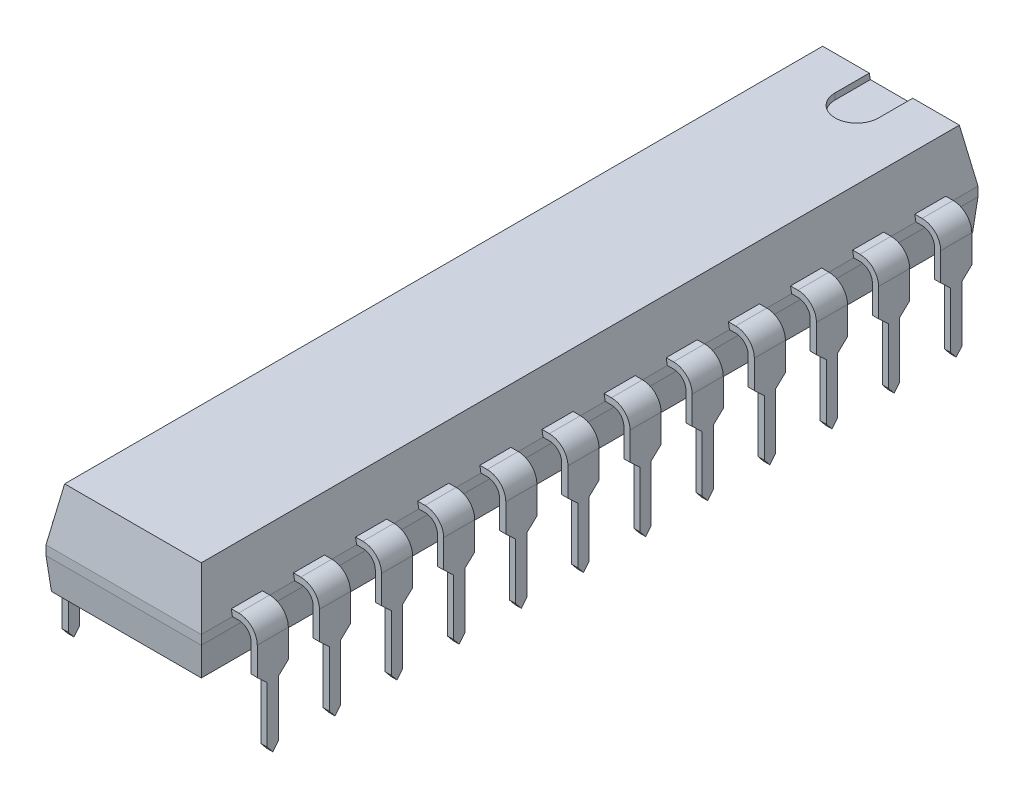
SolidWorks part; units mm, degrees
ref_plane "Front Plane" through (0, 0, 0) normal (0, 0, 1) x (1, 0, 0)
ref_plane "Top Plane" through (0, 0, 0) normal (0, 1, 0) x (1, 0, 0)
ref_plane "Right Plane" through (0, 0, 0) normal (1, 0, 0) x (0, 0, -1)
ref_plane "Plane4" through (0, 0.381, 0) normal (0, 1, 0) x (-1, 0, 0)
sketch "Sketch2" plane through (0, 0.381, 0) normal (0, 1, 0) x (0, 0, 1)
  line L1 (-1.905, 7.112) -> (29.845, 7.112)
  line L2 (-1.905, 7.112) -> (-1.905, 0.762)
  line L3 (-1.905, 0.762) -> (29.845, 0.762)
  line L4 (29.845, 7.112) -> (29.845, 0.762)
  dimension "D1" = 6.35
  dimension "D2" = 31.75
  dimension "D3" = 1.905
  dimension "D4" = 0.762
extrude "Base-Extrude" add sketch "Sketch2" along normal blind 3.81
chamfer "Chamfer1" distance 2.159 angle 10 4 edges at (3.937, 4.191, 29.845) (7.112, 4.191, 13.97) (3.937, 4.191, -1.905) (0.762, 4.191, 13.97)
chamfer "Chamfer2" distance 1.27 angle 5 4 edges at (7.112, 0.381, 13.97) (3.937, 0.381, 29.845) (0.762, 0.381, 13.97) (3.937, 0.381, -1.905)
sketch "Sketch3" plane through (0, 4.191, 0) normal (0, 1, 0) x (-1, 0, 0)
  line L0 (-0.762, -1.905) -> (-7.112, -1.905) construction
  line L1 (-3.048, -1.905) -> (-4.826, -1.905)
  line L2 (-3.937, -1.905) -> (-3.937, 1.8103) construction
  line L3 (-3.048, -1.905) -> (-3.048, -0.127)
  line L4 (-0.762, 29.845) -> (-0.762, -1.905) construction
  line L5 (-4.826, -1.905) -> (-4.826, -0.127)
  arc A0 (-3.048, -0.127) -> (-4.826, -0.127) centre (-3.937, -0.127) ccw
  dimension "D2" = 0.889
  dimension "D1" = 1.778
  dimension "D3" = 1.778
  dimension "D4" = 3.175
extrude "Cut-Extrude1" cut sketch "Sketch3" against normal blind 0.254
sketch "Sketch4" plane through (0, 0, 0) normal (0, 0, -1) x (-1, 0, 0)
  line L0 (-1.1903, 2.032) -> (-0.508, 2.032)
  line L1 (-0.762, 2.032) -> (-7.112, 2.032) construction
  line L2 (0, 1.524) -> (0, -2.5654)
  arc A0 (-0.508, 2.032) -> (0, 1.524) centre (-0.508, 1.524) cw
  dimension "D1" = 0.508
  dimension "D2" = 2.5654
extrude "Boss-Extrude-Thin1" add sketch "Sketch4" along normal mid plane 1.27 thin thin type one direction reverse wall 0.254
sketch "Sketch5" plane through (0, 0, 0) normal (1, 0, 0) x (0, 0, -1)
  line L0 (0.635, -2.5654) -> (-0.635, -2.5654) construction
  line L1 (-0.635, 1.524) -> (-0.635, -2.5654) construction
  line L2 (0, -2.5654) -> (-0.635, -2.5654)
  line L3 (-0.635, 0.381) -> (-0.635, -2.5654)
  line L4 (-0.635, 0.381) -> (-0.2286, 0)
  line L5 (-0.2286, 0) -> (-0.2286, -2.286)
  line L6 (-0.2286, -2.286) -> (0, -2.5654)
  line L7 (50, 0.381) -> (-50, 0.381) construction
  dimension "D1" = 0.2286
  dimension "D2" = 2.286
extrude "Cut-Extrude2" cut sketch "Sketch5" against normal through all
mirror "Mirror1" about plane through (0, 0, 0) normal (0, 0, 1) of "Cut-Extrude2"
ref_plane "Plane5" through (3.937, 0, 0) normal (-1, 0, 0) x (0, 0, 1)
pattern_linear "LPattern1" count 12 spacing 2.54 along (0, 0, 1) of "Cut-Extrude2", "Mirror1", "Boss-Extrude-Thin1"
mirror "Mirror2" about plane through (3.937, 0, 0) normal (-1, 0, 0) of "LPattern1", "Boss-Extrude-Thin1", "Cut-Extrude2", "Mirror1"
sketch "Component_Outline" plane through (0, 0, 0) normal (0, 1, 0) x (1, 0, 0)
  line L0 (0.762, -29.845) -> (0.762, -28.575)
  line L1 (0.762, -28.575) -> (-0.254, -28.575)
  line L2 (-0.254, -28.575) -> (-0.254, -27.305)
  line L3 (-0.254, -27.305) -> (0.762, -27.305)
  line L4 (0.762, -27.305) -> (0.762, -26.035)
  line L5 (0.762, -26.035) -> (-0.254, -26.035)
  line L6 (-0.254, -26.035) -> (-0.254, -24.765)
  line L7 (-0.254, -24.765) -> (0.762, -24.765)
  line L8 (0.762, -24.765) -> (0.762, -23.495)
  line L9 (0.762, -23.495) -> (-0.254, -23.495)
  line L10 (-0.254, -23.495) -> (-0.254, -22.225)
  line L11 (-0.254, -22.225) -> (0.762, -22.225)
  line L12 (0.762, -22.225) -> (0.762, -20.955)
  line L13 (0.762, -20.955) -> (-0.254, -20.955)
  line L14 (-0.254, -20.955) -> (-0.254, -19.685)
  line L15 (-0.254, -19.685) -> (0.762, -19.685)
  line L16 (0.762, -19.685) -> (0.762, -18.415)
  line L17 (0.762, -18.415) -> (-0.254, -18.415)
  line L18 (-0.254, -18.415) -> (-0.254, -17.145)
  line L19 (-0.254, -17.145) -> (0.762, -17.145)
  line L20 (0.762, -17.145) -> (0.762, -15.875)
  line L21 (0.762, -15.875) -> (-0.254, -15.875)
  line L22 (-0.254, -15.875) -> (-0.254, -14.605)
  line L23 (-0.254, -14.605) -> (0.762, -14.605)
  line L24 (0.762, -14.605) -> (0.762, -13.335)
  line L25 (0.762, -13.335) -> (-0.254, -13.335)
  line L26 (-0.254, -13.335) -> (-0.254, -12.065)
  line L27 (-0.254, -12.065) -> (0.762, -12.065)
  line L28 (0.762, -12.065) -> (0.762, -10.795)
  line L29 (0.762, -10.795) -> (-0.254, -10.795)
  line L30 (-0.254, -10.795) -> (-0.254, -9.525)
  line L31 (-0.254, -9.525) -> (0.762, -9.525)
  line L32 (0.762, -9.525) -> (0.762, -8.255)
  line L33 (0.762, -8.255) -> (-0.254, -8.255)
  line L34 (-0.254, -8.255) -> (-0.254, -6.985)
  line L35 (-0.254, -6.985) -> (0.762, -6.985)
  line L36 (0.762, -6.985) -> (0.762, -5.715)
  line L37 (0.762, -5.715) -> (-0.254, -5.715)
  line L38 (-0.254, -5.715) -> (-0.254, -4.445)
  line L39 (-0.254, -4.445) -> (0.762, -4.445)
  line L40 (0.762, -4.445) -> (0.762, -3.175)
  line L41 (0.762, -3.175) -> (-0.254, -3.175)
  line L42 (-0.254, -3.175) -> (-0.254, -1.905)
  line L43 (-0.254, -1.905) -> (0.762, -1.905)
  line L44 (0.762, -1.905) -> (0.762, -0.635)
  line L45 (0.762, -0.635) -> (-0.254, -0.635)
  line L46 (-0.254, -0.635) -> (-0.254, 0.635)
  line L47 (-0.254, 0.635) -> (0.762, 0.635)
  line L48 (0.762, 0.635) -> (0.762, 1.905)
  line L49 (3.937, -29.7339) -> (3.937, 1.905) construction
  line L50 (7.0009, -29.7339) -> (0.8731, -29.7339) construction
  line L51 (7.112, 1.905) -> (0.762, 1.905) construction
  line L52 (7.112, 0.635) -> (7.112, 1.905)
  line L53 (8.128, 0.635) -> (7.112, 0.635)
  line L54 (8.128, -0.635) -> (8.128, 0.635)
  line L55 (7.112, -0.635) -> (8.128, -0.635)
  line L56 (7.112, -1.905) -> (7.112, -0.635)
  line L57 (8.128, -1.905) -> (7.112, -1.905)
  line L58 (8.128, -3.175) -> (8.128, -1.905)
  line L59 (7.112, -3.175) -> (8.128, -3.175)
  line L60 (7.112, -4.445) -> (7.112, -3.175)
  line L61 (8.128, -4.445) -> (7.112, -4.445)
  line L62 (8.128, -5.715) -> (8.128, -4.445)
  line L63 (7.112, -5.715) -> (8.128, -5.715)
  line L64 (7.112, -6.985) -> (7.112, -5.715)
  line L65 (8.128, -6.985) -> (7.112, -6.985)
  line L66 (8.128, -8.255) -> (8.128, -6.985)
  line L67 (7.112, -8.255) -> (8.128, -8.255)
  line L68 (7.112, -9.525) -> (7.112, -8.255)
  line L69 (8.128, -9.525) -> (7.112, -9.525)
  line L70 (8.128, -10.795) -> (8.128, -9.525)
  line L71 (7.112, -10.795) -> (8.128, -10.795)
  line L72 (7.112, -12.065) -> (7.112, -10.795)
  line L73 (8.128, -12.065) -> (7.112, -12.065)
  line L74 (8.128, -13.335) -> (8.128, -12.065)
  line L75 (7.112, -13.335) -> (8.128, -13.335)
  line L76 (7.112, -14.605) -> (7.112, -13.335)
  line L77 (8.128, -14.605) -> (7.112, -14.605)
  line L78 (8.128, -15.875) -> (8.128, -14.605)
  line L79 (7.112, -15.875) -> (8.128, -15.875)
  line L80 (7.112, -17.145) -> (7.112, -15.875)
  line L81 (8.128, -17.145) -> (7.112, -17.145)
  line L82 (8.128, -18.415) -> (8.128, -17.145)
  line L83 (7.112, -18.415) -> (8.128, -18.415)
  line L84 (7.112, -19.685) -> (7.112, -18.415)
  line L85 (8.128, -19.685) -> (7.112, -19.685)
  line L86 (8.128, -20.955) -> (8.128, -19.685)
  line L87 (7.112, -20.955) -> (8.128, -20.955)
  line L88 (7.112, -22.225) -> (7.112, -20.955)
  line L89 (8.128, -22.225) -> (7.112, -22.225)
  line L90 (8.128, -23.495) -> (8.128, -22.225)
  line L91 (7.112, -23.495) -> (8.128, -23.495)
  line L92 (7.112, -24.765) -> (7.112, -23.495)
  line L93 (8.128, -24.765) -> (7.112, -24.765)
  line L94 (8.128, -26.035) -> (8.128, -24.765)
  line L95 (7.112, -26.035) -> (8.128, -26.035)
  line L96 (7.112, -27.305) -> (7.112, -26.035)
  line L97 (8.128, -27.305) -> (7.112, -27.305)
  line L98 (8.128, -28.575) -> (8.128, -27.305)
  line L99 (7.112, -28.575) -> (8.128, -28.575)
  line L100 (7.112, -29.845) -> (7.112, -28.575)
  line L101 (0.762, -29.845) -> (7.112, -29.845)
  line L102 (0.762, 1.905) -> (7.112, 1.905)
